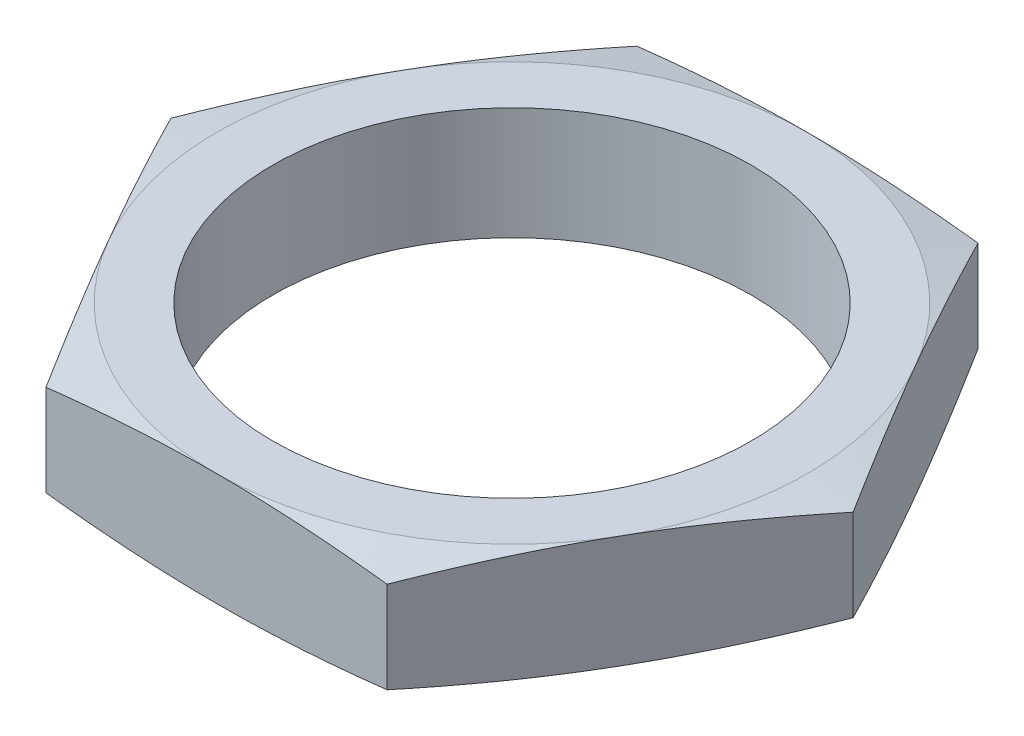
SolidWorks part; units mm, degrees
material "1060 Сплав"
ref_plane "Спереди" through (0, 0, 0) normal (0, 0, 1) x (1, 0, 0)
ref_plane "Сверху" through (0, 0, 0) normal (0, 1, 0) x (1, 0, 0)
ref_plane "Справа" through (0, 0, 0) normal (1, 0, 0) x (0, 0, -1)
sketch "Эскиз1" plane through (0, 0, 0) normal (0, 1, 0) x (1, 0, 0)
  line L1 (12.1244, 0) -> (6.0622, 10.5)
  line L2 (6.0622, 10.5) -> (-6.0622, 10.5)
  line L3 (-6.0622, 10.5) -> (-12.1244, 0)
  line L4 (-12.1244, 0) -> (-6.0622, -10.5)
  line L5 (-6.0622, -10.5) -> (6.0622, -10.5)
  line L6 (6.0622, -10.5) -> (12.1244, 0)
  circle A0 centre (0, 0) radius 10.5 construction
  circle A1 centre (0, 0) radius 8.5
  dimension "D1" = 21
  dimension "D2" = 17
extrude "Бобышка-Вытянуть1" add sketch "Эскиз1" along normal blind 4
cosmetic thread "Условное изображение резьбы1" parameters "D2"=18
sketch "Эскиз2" plane through (0, 4, 0) normal (0, 1, 0) x (1, 0, 0)
  line L0 (12.1244, 0) -> (6.0622, 10.5) construction
  circle A0 centre (0, 0) radius 10.5
extrude "Вырез-Вытянуть1" cut sketch "Эскиз2" against normal through all draft 77 flip side to cut
sketch "Эскиз3" plane through (0, 0, 0) normal (0, -1, 0) x (1, 0, 0)
  line L0 (-12.1244, 0) -> (-6.0622, 10.5) construction
  circle A0 centre (0, 0) radius 10.5
extrude "Вырез-Вытянуть2" cut sketch "Эскиз3" against normal through all draft 77 flip side to cut
